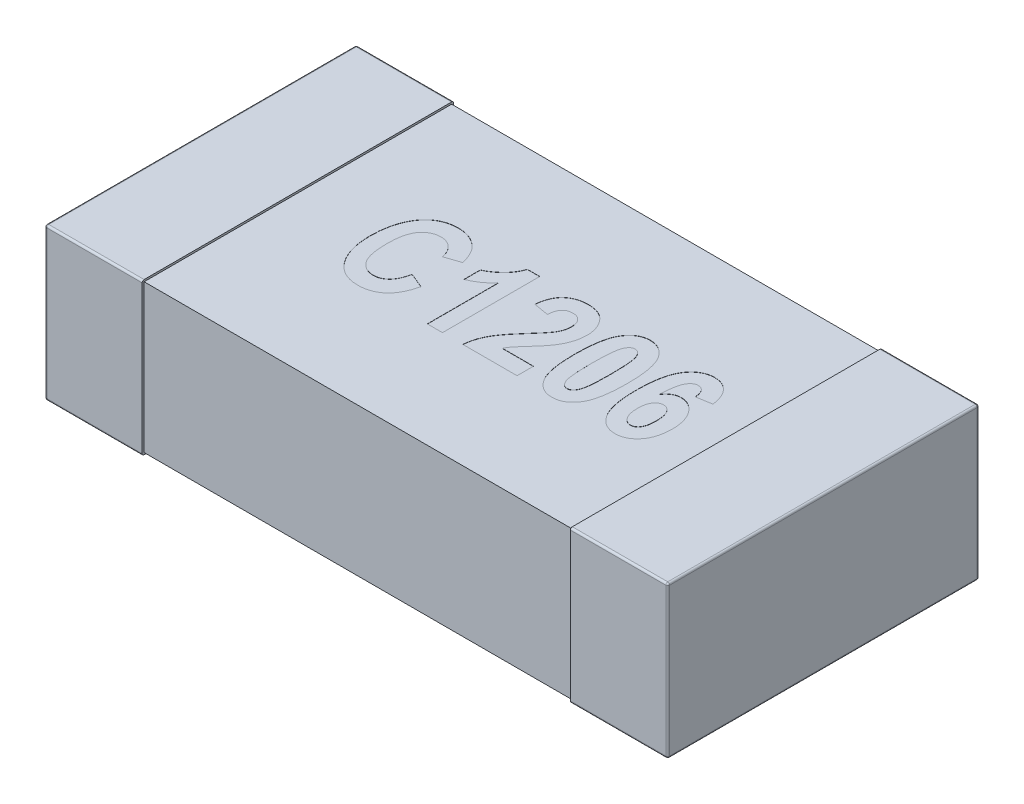
SolidWorks part; units mm, degrees
ref_plane "Front Plane" through (0, 0, 0) normal (0, 0, 1) x (1, 0, 0)
ref_plane "Top Plane" through (0, 0, 0) normal (0, 1, 0) x (1, 0, 0)
ref_plane "Right Plane" through (0, 0, 0) normal (1, 0, 0) x (0, 0, -1)
sketch "Sketch1" plane through (0, 0, 0) normal (0, 1, 0) x (1, 0, 0)
  line L0 (0, 0.15) -> (0, -0.15) construction
  line L1 (-1.6, 0) -> (0, 0) construction
  line L3 (-1.6, 0.8) -> (-1.1, 0.8)
  line L4 (-1.6, 0.8) -> (-1.6, -0.8)
  line L5 (-1.6, -0.8) -> (-1.1, -0.8)
  line L6 (-1.1, 0.8) -> (-1.1, -0.8)
  dimension "BANDWIDTH" = 0.5
  dimension "WIDTH" = 1.6
  dimension "LENGTH-HALF" = 1.6
extrude "THICKNESS" add sketch "Sketch1" along normal blind 0.78
fillet "Fillet1" radius 0.01 8 edges at (-1.6, 0, 0) (-1.35, 0, -0.8) (-1.6, 0.39, -0.8) (-1.35, 0, 0.8) (-1.6, 0.39, 0.8) (-1.6, 0.78, 0) (-1.35, 0.78, -0.8) (-1.35, 0.78, 0.8)
sketch "Sketch2" plane through (0, 0, 0) normal (1, 0, 0) x (0, 0, -1)
  line L0 (0, 0.78) -> (0, 0) construction
  line L1 (-0.79, 0.77) -> (0.79, 0.77)
  line L2 (-0.79, 0.77) -> (-0.79, 0.01)
  line L3 (-0.79, 0.01) -> (0.79, 0.01)
  line L4 (0.79, 0.77) -> (0.79, 0.01)
  line L5 (-0.79, 0.78) -> (0.79, 0.78) construction
  line L6 (-0.79, 0) -> (0.79, 0) construction
  line L7 (-0.8, 0.39) -> (0.8, 0.39) construction
  line L8 (-0.8, 0.77) -> (-0.8, 0.01) construction
  line L9 (0.8, 0.77) -> (0.8, 0.01) construction
  dimension "D1" = 0.01
  dimension "D2" = 0.01
extrude "Boss-Extrude2" add sketch "Sketch2" against normal up to surface (1.1 mm away) up to face at (-1.1, 0.39, 0)
mirror "Mirror3" about plane through (0, 0, 0) normal (1, 0, 0) of "Boss-Extrude2", "Fillet1", "THICKNESS"
sketch "Sketch3" plane through (0, 0.77, 0) normal (0, 1, 0) x (1, 0, 0)
  line L0 (-0.75, -0.25) -> (0.75, -0.25) construction
  line L1 (0, -0.429) -> (0, 0.429) construction
  line L2 (-0.429, 0) -> (0.429, 0) construction
  text T0 "<b>C1206</b>" font "Arial Narrow" height 0.5
  point P2 (0, -0.25)
  dimension "D1" = 1.5
  dimension "D2" = 0.25
extrude "Cut-Extrude1" cut sketch "Sketch3" against normal blind 0.001
